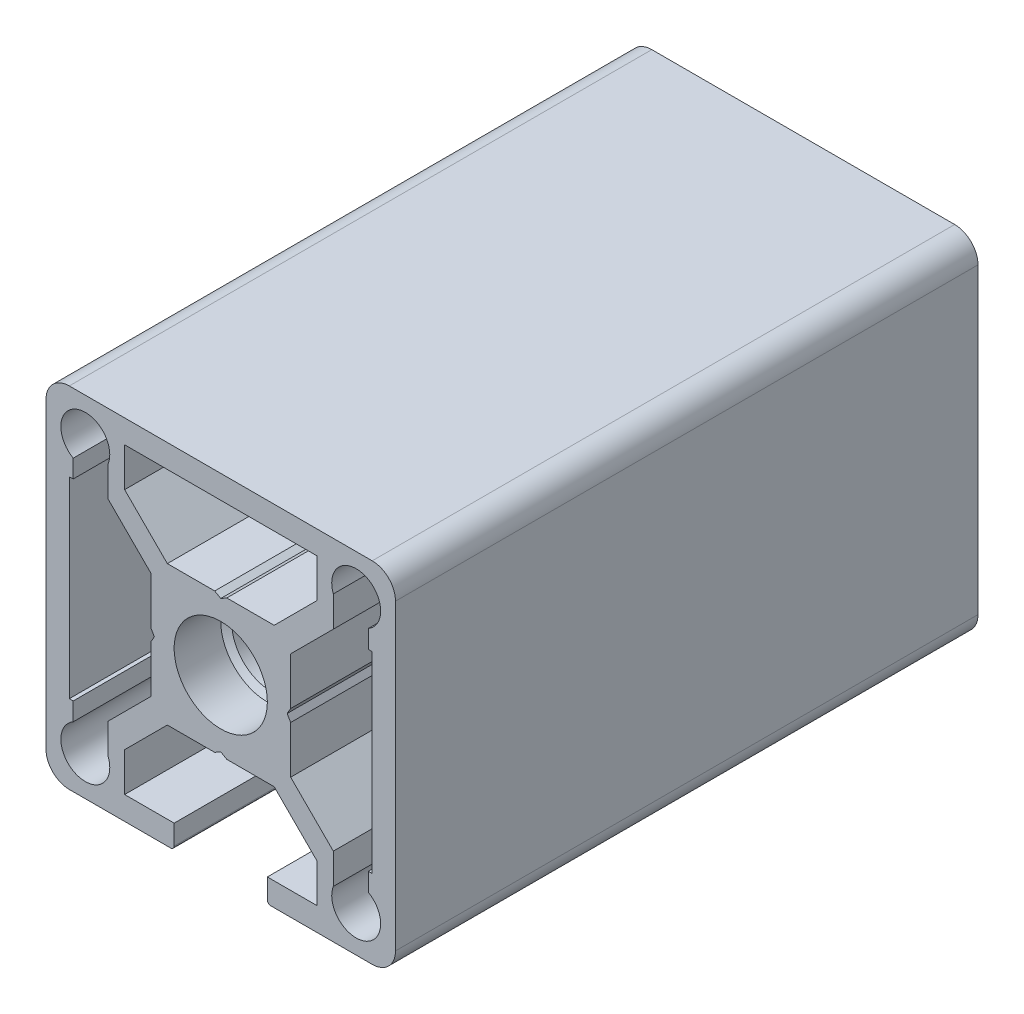
SolidWorks part; units mm, degrees
ref_plane "Front Plane" through (0, 0, 0) normal (0, 0, 1) x (1, 0, 0)
ref_plane "Top Plane" through (0, 0, 0) normal (0, 1, 0) x (1, 0, 0)
ref_plane "Right Plane" through (0, 0, 0) normal (1, 0, 0) x (0, 0, -1)
ref_plane "Plane1" through (0, 0, 0) normal (0, 0, 1) x (1, 0, 0)
sketch "Sketch1" plane through (0, 0, 0) normal (0, 0, 1) x (1, 0, 0)
  line L0 (-15, 13) -> (-15, 4.3)
  line L1 (-14.7, 4) -> (-13, 4)
  line L2 (-13, 4) -> (-13, 8.25)
  line L3 (-13, 8.25) -> (-9.6642, 8.25)
  line L4 (-9.6642, 8.25) -> (-6, 4.5858)
  line L5 (-6, 4.5858) -> (-6, 0.5196)
  line L6 (-6, 0.5196) -> (-5.7, 0)
  line L7 (-5.7, 0) -> (-6, -0.5196)
  line L8 (-6, -0.5196) -> (-6, -4.5858)
  line L9 (-6, -4.5858) -> (-9.6642, -8.25)
  line L10 (-9.6642, -8.25) -> (-13, -8.25)
  line L11 (-13, -8.25) -> (-13, -4)
  line L12 (-13, -4) -> (-14.7, -4)
  line L13 (-15, -4.3) -> (-15, -13)
  line L14 (-13, -15) -> (-4.3, -15)
  line L15 (-4, -14.7) -> (-4, -13)
  line L16 (-4, -13) -> (-8.25, -13)
  line L17 (-8.25, -13) -> (-8.25, -9.6642)
  line L18 (-8.25, -9.6642) -> (-4.5858, -6)
  line L19 (-4.5858, -6) -> (-0.5196, -6)
  line L20 (-0.5196, -6) -> (0, -5.7)
  line L21 (0, -5.7) -> (0.5196, -6)
  line L22 (0.5196, -6) -> (4.5858, -6)
  line L23 (4.5858, -6) -> (8.25, -9.6642)
  line L24 (8.25, -9.6642) -> (8.25, -13)
  line L25 (8.25, -13) -> (4, -13)
  line L26 (4, -13) -> (4, -14.7)
  line L27 (4.3, -15) -> (13, -15)
  line L28 (15, -13) -> (15, -4.3)
  line L29 (14.7, -4) -> (13, -4)
  line L30 (13, -4) -> (13, -8.25)
  line L31 (13, -8.25) -> (9.6642, -8.25)
  line L32 (9.6642, -8.25) -> (6, -4.5858)
  line L33 (6, -4.5858) -> (6, -0.5196)
  line L34 (6, -0.5196) -> (5.7, 0)
  line L35 (5.7, 0) -> (6, 0.5196)
  line L36 (6, 0.5196) -> (6, 4.5858)
  line L37 (6, 4.5858) -> (9.6642, 8.25)
  line L38 (9.6642, 8.25) -> (13, 8.25)
  line L39 (13, 8.25) -> (13, 4)
  line L40 (13, 4) -> (14.7, 4)
  line L41 (15, 4.3) -> (15, 13)
  line L42 (13, 15) -> (4.3, 15)
  line L43 (4, 14.7) -> (4, 13)
  line L44 (4, 13) -> (8.25, 13)
  line L45 (8.25, 13) -> (8.25, 9.6642)
  line L46 (8.25, 9.6642) -> (4.5858, 6)
  line L47 (4.5858, 6) -> (0.5196, 6)
  line L48 (0.5196, 6) -> (0, 5.7)
  line L49 (0, 5.7) -> (-0.5196, 6)
  line L50 (-0.5196, 6) -> (-4.5858, 6)
  line L51 (-4.5858, 6) -> (-8.25, 9.6642)
  line L52 (-8.25, 9.6642) -> (-8.25, 13)
  line L53 (-8.25, 13) -> (-4, 13)
  line L54 (-4, 13) -> (-4, 14.7)
  line L55 (-4.3, 15) -> (-13, 15)
  arc A0 (-15, 4.3) -> (-14.7, 4) centre (-14.7, 4.3) ccw
  arc A1 (-14.7, -4) -> (-15, -4.3) centre (-14.7, -4.3) ccw
  arc A2 (-15, -13) -> (-13, -15) centre (-13, -13) ccw
  arc A3 (-4.3, -15) -> (-4, -14.7) centre (-4.3, -14.7) ccw
  arc A4 (4, -14.7) -> (4.3, -15) centre (4.3, -14.7) ccw
  arc A5 (13, -15) -> (15, -13) centre (13, -13) ccw
  arc A6 (15, -4.3) -> (14.7, -4) centre (14.7, -4.3) ccw
  arc A7 (14.7, 4) -> (15, 4.3) centre (14.7, 4.3) ccw
  arc A8 (15, 13) -> (13, 15) centre (13, 13) ccw
  arc A9 (4.3, 15) -> (4, 14.7) centre (4.3, 14.7) ccw
  arc A10 (-4, 14.7) -> (-4.3, 15) centre (-4.3, 14.7) ccw
  arc A11 (-13, 15) -> (-15, 13) centre (-13, 13) ccw
  circle A12 centre (11.625, -11.625) radius 2.1
  circle A13 centre (11.625, 11.625) radius 2.1
  circle A14 centre (0, 0) radius 3.4
  circle A15 centre (-11.625, -11.625) radius 2.1
  circle A16 centre (-11.625, 11.625) radius 2.1
extrude "Boss-Extrude1" add sketch "Sketch1" against normal blind 50
cosmetic thread "Cosmetic Thread1" parameters "D1"=24, "D2"=8
ref_plane "Plane2" through (0, 0, 0) normal (0, 1, 0) x (-1, 0, 0)
sketch "Sketch2" plane through (0, 0, 0) normal (0, 1, 0) x (-1, 0, 0)
  line L0 (0, -28.3188) -> (-3.3235, -26.4)
  line L1 (-3.3235, -26.4) -> (-3.3235, -0.6765)
  line L2 (-3.3235, -0.6765) -> (-4, 0)
  line L3 (-4, 0) -> (0, 0)
  line L4 (0, 0) -> (0, -28.3188)
  line L5 (0, 0) -> (0, -28.3188) construction
revolve "Cut-Revolve1" cut sketch "Sketch2" angle 360 about L5
sketch "Sketch3" plane through (0, 0, 0) normal (0, 0, 1) x (1, 0, 0)
  line L0 (-13, -8.25) -> (-13, -4) construction
  line L1 (-15, 4.3) -> (-13, 4.3)
  line L2 (-15, 4.3) -> (-15, -4.8752)
  line L3 (-15, -4.8752) -> (-13, -4.8752)
  line L4 (-13, 4.3) -> (-13, -4.8752)
  line L5 (-4.3, 15) -> (-13, 15) construction
  line L6 (-6.182, 15) -> (4.8944, 15)
  line L7 (-6.182, 15) -> (-6.182, 13)
  line L8 (-6.182, 13) -> (4.8944, 13)
  line L9 (4.8944, 15) -> (4.8944, 13)
  line L10 (4, 13) -> (8.25, 13) construction
  line L11 (13, 8.25) -> (13, 4) construction
  line L12 (13, 5.5647) -> (15, 5.5647)
  line L13 (13, 5.5647) -> (13, -6.3507)
  line L14 (13, -6.3507) -> (15, -6.3507)
  line L15 (15, 5.5647) -> (15, -6.3507)
  line L16 (15, -13) -> (15, -4.3) construction
extrude "Boss-Extrude2" add sketch "Sketch3" against normal up to surface (50 mm away) up to face at (-9.525, 11.625, -50)
sketch "Sketch4" plane through (0, 0, 0) normal (0, 0, 1) x (1, 0, 0)
  line L1 (12.6642, 10.8732) -> (9.6642, 10.8732)
  line L2 (12.6642, 10.8732) -> (12.6642, -10.8732)
  line L3 (12.6642, -10.8732) -> (9.6642, -10.8732)
  line L4 (9.6642, 10.8732) -> (9.6642, -10.8732)
  line L5 (-12.6642, 10.8732) -> (-9.6642, 10.8732)
  line L6 (-12.6642, 10.8732) -> (-12.6642, -10.8732)
  line L7 (-12.6642, -10.8732) -> (-9.6642, -10.8732)
  line L8 (-9.6642, 10.8732) -> (-9.6642, -10.8732)
  circle A4 centre (-11.625, 11.625) radius 2.1 construction
  circle A5 centre (-11.625, -11.625) radius 2.1 construction
  circle A6 centre (11.625, -11.625) radius 2.1 construction
  circle A7 centre (11.625, 11.625) radius 2.1 construction
  dimension "D1" = 3
  dimension "D2" = 3
extrude "Cut-Extrude1" cut sketch "Sketch4" against normal through all
sketch "Sketch5" plane through (0, 0, 0) normal (1, 0, 0) x (0, 0, -1)
  line L0 (0, 0) -> (71.4956, 0) construction
  line L1 (0, 0) -> (0, 4)
  line L2 (4, 4) -> (0, 4)
  line L3 (4, 4) -> (6.3094, 0)
  line L4 (6.3094, 0) -> (0, 0)
  dimension "D1" = 60
  dimension "D2" = 4
revolve "Cut-Revolve5" cut sketch "Sketch5" angle 360 about L0
